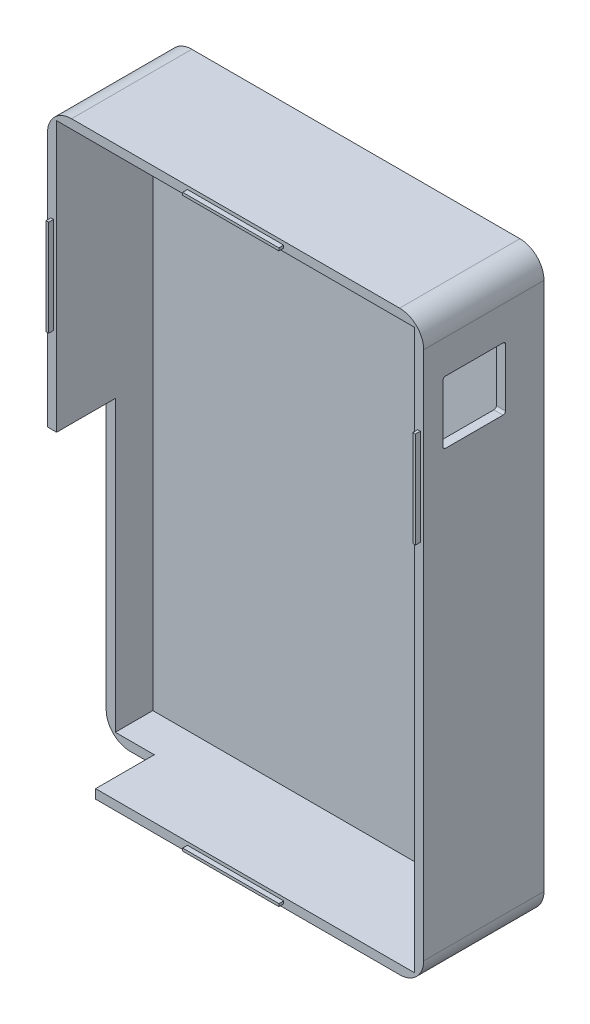
SolidWorks part; units mm, degrees
ref_plane "Piano frontale" through (0, 0, 0) normal (0, 0, 1) x (1, 0, 0)
ref_plane "Piano superiore" through (0, 0, 0) normal (0, 1, 0) x (1, 0, 0)
ref_plane "Piano destro" through (0, 0, 0) normal (1, 0, 0) x (0, 0, -1)
sketch "Schizzo1" plane through (0, 0, 0) normal (0, 0, 1) x (1, 0, 0)
  line L1 (-39.1, 41.1639) -> (39.1, 41.1639)
  line L2 (-39.1, 41.1639) -> (-39.1, -78.8361)
  line L3 (-39.1, -78.8361) -> (39.1, -78.8361)
  line L4 (39.1, 41.1639) -> (39.1, -78.8361)
  point P4 (0, 41.1639)
  dimension "D1" = 78.2
  dimension "D2" = 120
extrude "Estrusione-Estrusione1" add sketch "Schizzo1" along normal blind 5
sketch "Schizzo2" plane through (0, 0, 5) normal (0, 0, 1) x (1, 0, 0)
  line L1 (-39.1, 41.1639) -> (39.1, 41.1639)
  line L2 (-39.1, 41.1639) -> (-39.1, -78.8361)
  line L3 (-39.1, -78.8361) -> (39.1, -78.8361)
  line L4 (39.1, 41.1639) -> (39.1, -78.8361)
  line L5 (-37.2, 39.2639) -> (37.2, 39.2639)
  line L6 (-37.2, 39.2639) -> (-37.2, -76.9361)
  line L7 (-37.2, -76.9361) -> (37.2, -76.9361)
  line L8 (37.2, 39.2639) -> (37.2, -76.9361)
  dimension "D1" = 1.9
  dimension "D2" = 1.9
  dimension "D3" = 1.9
  dimension "D4" = 1.9
extrude "Estrusione-Estrusione2" add sketch "Schizzo2" along normal blind 20
sketch "Schizzo3" plane through (0, 0, 25) normal (0, 0, 1) x (1, 0, 0)
  line L1 (-38.4, 21.1639) -> (-37.85, 21.1639)
  line L2 (-38.4, 21.1639) -> (-38.4, 1.1639)
  line L3 (-38.4, 1.1639) -> (-37.85, 1.1639)
  line L4 (-37.85, 21.1639) -> (-37.85, 1.1639)
  line L5 (37.8521, 21.1639) -> (38.4021, 21.1639)
  line L6 (37.8521, 21.1639) -> (37.8521, 1.1639)
  line L7 (37.8521, 1.1639) -> (38.4021, 1.1639)
  line L8 (38.4021, 21.1639) -> (38.4021, 1.1639)
  line L9 (39.1, -78.8361) -> (39.1, 41.1639) construction
  line L10 (-10, 40.4639) -> (10, 40.4639)
  line L11 (-10, 40.4639) -> (-10, 39.9139)
  line L12 (-10, 39.9139) -> (10, 39.9139)
  line L13 (10, 40.4639) -> (10, 39.9139)
  line L14 (-10, -77.5861) -> (10, -77.5861)
  line L15 (-10, -77.5861) -> (-10, -78.1361)
  line L16 (-10, -78.1361) -> (10, -78.1361)
  line L17 (10, -77.5861) -> (10, -78.1361)
  line L18 (-39.1, 41.1639) -> (-39.1, -78.8361) construction
  line L19 (39.1, 41.1639) -> (-39.1, 41.1639) construction
  line L20 (-39.1, -78.8361) -> (39.1, -78.8361) construction
  point P24 (-37.85, 11.1639)
  point P25 (37.8521, 11.1639)
  point P26 (0, 40.4639)
  point P28 (0, -77.5861)
  dimension "D1" = 20
  dimension "D2" = 20
  dimension "D3" = 20
  dimension "D4" = 20
  dimension "D5" = 0.55
  dimension "D6" = 0.6979
  dimension "D7" = 0.55
  dimension "D8" = 0.7
  dimension "D9" = 0.55
  dimension "D10" = 0.7
  dimension "D11" = 0.55
  dimension "D12" = 0.7
  dimension "D13" = 20
extrude "Estrusione-Estrusione3" add sketch "Schizzo3" along normal blind 1
sketch "Schizzo4" plane through (39.1, 0, 0) normal (1, 0, 0) x (0, 0, -1)
  line L0 (-25, 41.1639) -> (0, 41.1639) construction
  line L1 (-21, 29.1639) -> (-8, 29.1639)
  line L2 (-21, 29.1639) -> (-21, 16.1639)
  line L3 (-21, 16.1639) -> (-8, 16.1639)
  line L4 (-8, 29.1639) -> (-8, 16.1639)
  line L5 (-25, -78.8361) -> (-25, 41.1639) construction
  dimension "D1" = 12
  dimension "D2" = 13
  dimension "D3" = 4
  dimension "D4" = 13
extrude "Taglio-Estrusione1" cut sketch "Schizzo4" against normal blind 4
fillet "Raccordo1" radius 5 4 edges at (39.1, -78.8361, 12.5) (-39.1, -78.8361, 12.5) (-39.1, 41.1639, 12.5) (39.1, 41.1639, 12.5)
fillet "Raccordo2" radius 0.5 4 edges at (38.15, 16.1639, 21) (38.15, 29.1639, 21) (38.15, 16.1639, 8) (38.15, 29.1639, 8)
sketch "Schizzo5" plane through (-39.1, 0, 0) normal (-1, 0, 0) x (0, 0, 1)
  line L1 (25, -78.8361) -> (12.8, -78.8361)
  line L2 (25, -78.8361) -> (25, -16.8361)
  line L3 (25, -16.8361) -> (12.8, -16.8361)
  line L4 (12.8, -78.8361) -> (12.8, -16.8361)
  dimension "D1" = 62
  dimension "D2" = 12.2
extrude "Taglio-Estrusione2" cut sketch "Schizzo5" against normal blind 10
